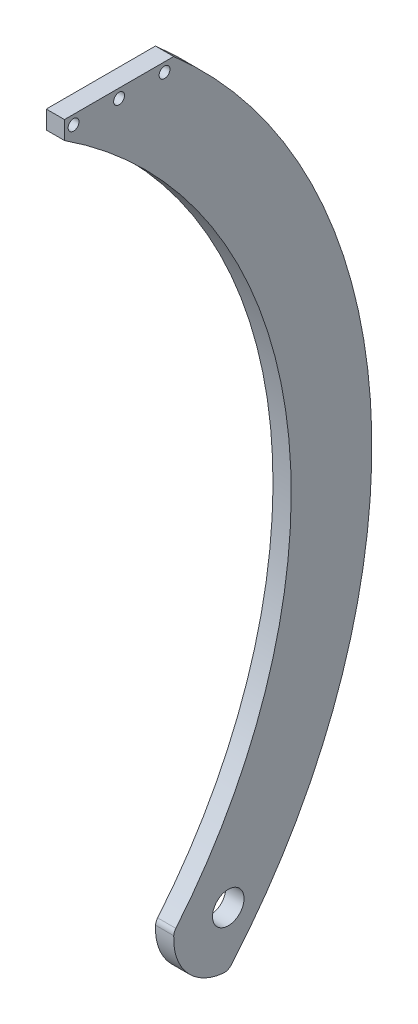
SolidWorks part; units mm, degrees
material "6061-T6 (SS)"
ref_plane "Front Plane" through (0, 0, 0) normal (0, 0, 1) x (1, 0, 0)
ref_plane "Top Plane" through (0, 0, 0) normal (0, 1, 0) x (1, 0, 0)
ref_plane "Right Plane" through (0, 0, 0) normal (1, 0, 0) x (0, 0, -1)
sketch "Sketch1" plane through (0, 0, 0) normal (1, 0, 0) x (0, 0, -1)
  line L0 (0, 266.7) -> (0, -149.8368) construction
  line L1 (0, 0) -> (38.1, 0) construction
  line L2 (-19.05, 266.7) -> (19.05, 266.7)
  line L3 (-19.05, 266.7) -> (-19.05, 260.35)
  arc A0 (0, 266.7) -> (0, -38.1) centre (-114.3, 114.3) cw construction
  arc A1 (-19.05, 260.35) -> (19.8048, 2.8591) centre (-114.3, 114.3) cw
  arc A2 (19.05, 266.7) -> (39.1106, -17.8861) centre (-114.3, 114.3) cw
  circle A3 centre (38.1, 0) radius 5.5
  arc A4 (19.076, 0.9959) -> (36.4264, -18.9763) centre (38.1, 0) ccw
  arc A5 (36.4264, -18.9763) -> (39.1106, -17.8861) centre (36.7053, -15.8136) ccw
  arc A6 (19.076, 0.9959) -> (19.8048, 2.8591) centre (22.2467, 0.8299) cw
  point P10 (0, 266.7)
  dimension "D3" = 190.5
  dimension "D5" = 6.35
  dimension "D6" = 11
  dimension "D7" = 38.1
  dimension "D8" = 3.175
  dimension "D1" = 38.1
  dimension "D2" = 266.7
  dimension "D4" = 38.1
extrude "Boss-Extrude1" add sketch "Sketch1" along normal blind 6.35
hole_wizard "#6 Clearance Hole1" positions "Sketch2" profile "Sketch3" hole size "#6" standard "ANSI Inch" end condition up to next
sketch "Sketch2" plane through (6.35, 0, 0) normal (1, 0, 0) x (0, 0, -1)
  line L2 (-19.05, 266.7) -> (-19.05, 260.35) construction
  line L3 (19.05, 266.7) -> (-19.05, 266.7) construction
  point P0 (-15.875, 263.525)
  point P2 (0, 263.525)
  point P4 (15.875, 263.525)
  dimension "D1" = 3.175
  dimension "D2" = 15.875
  dimension "D3" = 31.75
  dimension "D4" = 3.175
sketch "Sketch3" plane through (6.35, 263.525, 15.875) normal (0, 1, 0) x (0, 0, -1)
  line L0 (0, 0) -> (0, 6.35)
  line L1 (0, 6.35) -> (1.8986, 6.35)
  line L2 (1.8986, 6.35) -> (1.8986, 0)
  line L5 (1.8986, 0) -> (0, 0)
  line L11 (0, -6.35) -> (0, 107.95) construction
  dimension "Thru Hole Dia." = 3.7973
  dimension "Thru Hole Depth" = 6.35
